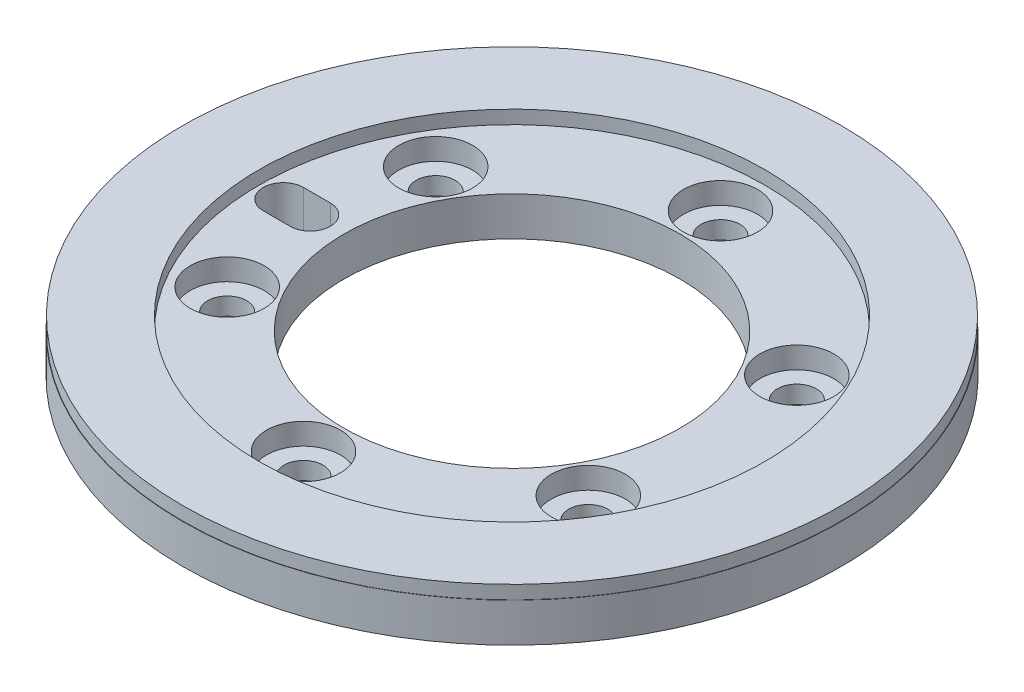
SolidWorks part; units mm, degrees
material "Chrome Stainless Steel"
ref_plane "Front Plane" through (0, 0, 0) normal (0, 0, 1) x (1, 0, 0)
ref_plane "Top Plane" through (0, 0, 0) normal (0, 1, 0) x (1, 0, 0)
ref_plane "Right Plane" through (0, 0, 0) normal (1, 0, 0) x (0, 0, -1)
sketch "Sketch1" plane through (0, 0, 0) normal (0, 0, 1) x (1, 0, 0)
  line L0 (0, -3.2439) -> (0, 13.5479) construction
  line L1 (-12.5, 0) -> (-24.5, 0)
  line L2 (-12.5, 0) -> (-12.5, 2.9)
  line L3 (-12.5, 2.9) -> (-24.5, 2.9)
  line L4 (-24.5, 0) -> (-24.5, 2.9)
  line L5 (-12.5, 0) -> (0, 0) construction
  dimension "D1" = 25
  dimension "D2" = 49
  dimension "D3" = 2.9
revolve "Revolve1" add sketch "Sketch1" angle 360 about L0
ref_plane "Plane1" through (0, 3.4, 0) normal (0, 1, 0) x (-1, 0, 0)
sketch "Sketch5" plane through (0, 2.9, 0) normal (0, 1, 0) x (1, 0, 0)
  circle A0 centre (0, 0) radius 18.8
  circle A1 centre (0, 0) radius 24.475
  dimension "D1" = 37.6
  dimension "D2" = 48.95
hole_wizard "CBORE for M2.5 Hex Socket Head Cap Screw2" positions "Sketch9" profile "Sketch8" counterbore size "M2.5" standard "DIN" end condition through all
sketch "Sketch9" plane through (0, 3.4, 0) normal (0, 1, 0) x (-1, 0, 0)
  line L0 (-46.9378, 0) -> (52.7339, 0) construction
  point P2 (0, -15.5)
  dimension "D1" = 31
sketch "Sketch8" plane through (0, 3.4, -15.5) normal (1, 0, 0) x (0, 0, 1)
  line L0 (0, 0) -> (0, 3.4)
  line L1 (0, 3.4) -> (1.45, 3.4)
  line L3 (1.45, 3.4) -> (1.45, 2.1)
  line L4 (1.45, 2.1) -> (2.75, 2.1)
  line L5 (2.75, 2.1) -> (2.75, 0)
  line L7 (2.75, 0) -> (0, 0)
  line L11 (0, -6.35) -> (0, 107.95) construction
  dimension "Thru Hole Dia." = 2.9
  dimension "Thru Hole Depth" = 3.4
  dimension "C'Bore Dia." = 5.5
  dimension "C'Bore Depth" = 2.1
pattern_circular "CirPattern1" count 6 over 360 about axis through (0, 0, 0) along (0, 1, 0) of "CBORE for M2.5 Hex Socket Head Cap Screw2"
sketch "Sketch10" plane through (0, 2.9, 0) normal (0, 1, 0) x (1, 0, 0)
  line L0 (0, 0) -> (-15, 0) construction
  line L1 (-15, 0) -> (-17, 0) construction
  line L2 (-15, -1.5) -> (-17, -1.5)
  line L3 (-15, 1.5) -> (-17, 1.5)
  arc A0 (-15, -1.5) -> (-15, 1.5) centre (-15, 0) ccw
  arc A1 (-17, 1.5) -> (-17, -1.5) centre (-17, 0) ccw
  point P3 (-16, 0)
  dimension "D1" = 15
  dimension "D2" = 2
  dimension "D3" = 3
extrude "Cut-Extrude4" cut sketch "Sketch10" against normal through all
extrude "Boss-Extrude1" add sketch "Sketch5" along normal blind 1
